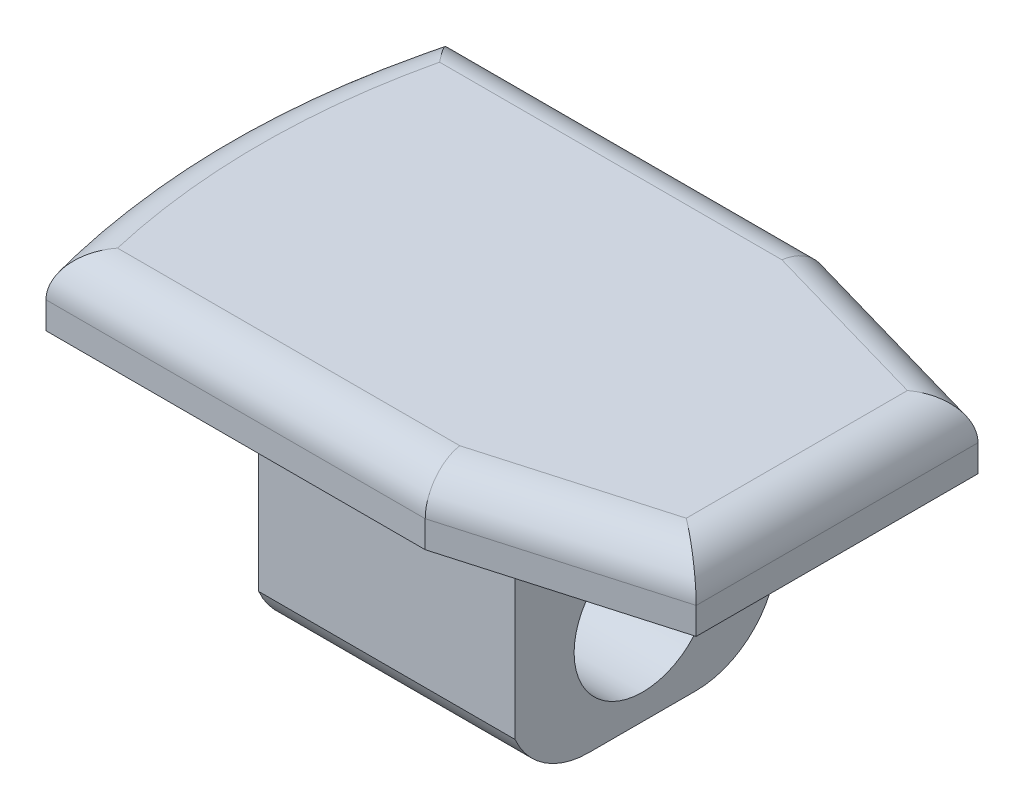
SolidWorks part; units mm, degrees
ref_plane "Front Plane" through (0, 0, 0) normal (0, 0, 1) x (1, 0, 0)
ref_plane "Top Plane" through (0, 0, 0) normal (0, 1, 0) x (1, 0, 0)
ref_plane "Right Plane" through (0, 0, 0) normal (1, 0, 0) x (0, 0, -1)
sketch "Sketch1" plane through (0, 0, 0) normal (0, 1, 0) x (1, 0, 0)
  line L0 (-34.3395, 50.6226) -> (-20.2094, 50.6226)
  line L1 (-20.2094, 50.6226) -> (-12.3627, 48.3726)
  line L2 (-12.3627, 48.3726) -> (-12.3627, 37.8726)
  line L3 (-12.3627, 37.8726) -> (-20.2094, 35.6226)
  line L4 (-20.2094, 35.6226) -> (-34.3395, 35.6226)
  line L5 (-29.3001, 48.1226) -> (-19.3627, 48.1226)
  line L6 (-19.3627, 48.1226) -> (-19.3627, 38.1226)
  line L7 (-19.3627, 38.1226) -> (-29.3001, 38.1226)
  circle A0 centre (-7.3627, 43.1226) radius 28
  circle A1 centre (-7.3627, 43.1226) radius 26
  point P13 (0, 0)
  point P14 (-7.3627, 43.1226)
  point P15 (0, 0)
  point P16 (-34.3395, 50.6226)
  point P17 (0, 0)
  point P18 (-34.3395, 35.6226)
extrude "Boss-Extrude1" add sketch "Sketch1" along normal blind 2.5 contours L0 A1 L5 L6 L7 L4 L3 L2 L1 | A1 L0 A0 L4
ref_plane "Plane1" through (-12.3627, 0, -37.8726) normal (0, 0, 1) x (1, 0, 0)
sketch "Sketch4" plane through (0, 0, 0) normal (0, -1, 0) x (1, 0, 0)
  line L0 (-35.3627, -43.1226) -> (3.6803, -43.1226) construction
  line L1 (-12.3627, -48.3726) -> (-12.3627, -37.8726) construction
  line L2 (-32.8774, -38.1226) -> (-19.3627, -38.1226)
  line L3 (-19.3627, -38.1226) -> (-19.3627, -48.1226)
  line L4 (-19.3627, -48.1226) -> (-32.8774, -48.1226)
  arc A0 (-34.3395, -35.6226) -> (-34.3395, -50.6226) centre (-7.3627, -43.1226) ccw construction
  circle A1 centre (-7.3627, -43.1226) radius 26
  point P5 (-7.3627, -43.1226)
  point P14 (-29.3001, -48.1226)
  point P19 (-29.3001, -38.1226)
  point P20 (0, 0)
  point P21 (0, 0)
  point P22 (-32.8774, -48.1226)
  point P23 (-30.3036, -38.1226)
  point P24 (-32.8774, -38.1226)
  dimension "D1" = 5
extrude "Boss-Extrude2" add sketch "Sketch4" along normal blind 1.5 and the other way blind 1.5
fillet "Fillet1" radius 1.5 6 edges at (-16.286, 2.5, -49.4976) (-12.3627, 2.5, -43.1226) (-16.286, 2.5, -36.7476) (-27.2745, 2.5, -35.6226) (-35.3627, 2.5, -43.1226) (-27.2745, 2.5, -50.6226)
sketch "Sketch5" plane through (0, -1.5, 0) normal (0, -1, 0) x (1, 0, 0)
  line L0 (-29.3001, -38.1226) -> (-19.3627, -38.1226) construction
  line L1 (-19.3627, -48.1226) -> (-29.1627, -48.1226)
  line L2 (-19.3627, -48.1226) -> (-19.3627, -38.1226)
  line L3 (-19.3627, -38.1226) -> (-29.1627, -38.1226)
  line L4 (-29.1627, -48.1226) -> (-29.1627, -38.1226)
  dimension "D1" = 9.8
extrude "Boss-Extrude3" add sketch "Sketch5" along normal blind 7.5
sketch "Sketch6" plane through (-19.3627, 0, 0) normal (1, 0, 0) x (0, 0, -1)
  line L0 (43.1226, 0) -> (43.1226, -9) construction
  line L1 (48.1226, 0) -> (38.1226, 0) construction
  line L2 (48.1226, -9) -> (38.1226, -9) construction
  circle A0 centre (43.1226, -5.5) radius 2.55
  dimension "D1" = 5.5
extrude "Cut-Extrude1" cut sketch "Sketch6" against normal blind 8
sketch "Sketch7" plane through (-27.3627, 0, 0) normal (1, 0, 0) x (0, 0, -1)
  line L1 (39.7279, -4.25) -> (47.1506, -4.25)
  line L2 (39.7279, -4.25) -> (39.7279, -6.75)
  line L3 (39.7279, -6.75) -> (47.1506, -6.75)
  line L4 (47.1506, -4.25) -> (47.1506, -6.75)
  circle A0 centre (43.1226, -5.5) radius 3
  dimension "D1" = 2.5
  dimension "D2" = 1.25
fillet "Fillet2" radius 3 2 edges at (-24.2627, -9, -48.1226) (-24.2627, -9, -38.1226)
sketch "Sketch8" plane through (-29.1627, 0, 0) normal (-1, 0, 0) x (0, 0, 1)
  circle A0 centre (-43.1226, -5.5) radius 2.6
  circle A1 centre (-43.1226, -5.5) radius 3
extrude "Boss-Extrude4" add sketch "Sketch8" against normal blind 0.8
sketch "Sketch9" plane through (0, -9, 0) normal (0, -1, 0) x (-1, 0, 0)
  line L0 (19.3627, 43.1226) -> (33.294, 43.1226) construction
  line L1 (19.3627, 48.1226) -> (19.3627, 38.1226) construction
  line L3 (28.406, 45.8226) -> (29.1627, 45.8226)
  line L4 (28.406, 45.8226) -> (28.406, 40.4226)
  line L5 (28.406, 40.4226) -> (29.1627, 40.4226)
  line L6 (29.1627, 45.8226) -> (29.1627, 40.4226)
  dimension "D1" = 2.7
  dimension "D2" = 2.7
extrude "Cut-Extrude3" cut sketch "Sketch9" against normal blind 3
sketch "Sketch10" plane through (-27.3627, 0, 0) normal (1, 0, 0) x (0, 0, -1)
  circle A0 centre (43.1226, -5.5) radius 3
extrude "Cut-Extrude4" cut sketch "Sketch10" against normal blind 3
sketch "Sketch11" plane through (0, 0, 0) normal (0, -1, 0) x (1, 0, 0)
  line L0 (-19.3627, -38.1226) -> (-32.8774, -38.1226)
  line L1 (-32.8774, -48.1226) -> (-19.3627, -48.1226)
  line L2 (-19.3627, -48.1226) -> (-19.3627, -38.1226)
  line L3 (-19.6127, -38.3726) -> (-32.6708, -38.3726)
  line L4 (-32.6708, -47.8726) -> (-19.6127, -47.8726)
  line L5 (-19.6127, -47.8726) -> (-19.6127, -38.3726)
  arc A0 (-32.8774, -38.1226) -> (-32.8774, -48.1226) centre (-7.3627, -43.1226) ccw
  arc A1 (-32.6708, -38.3726) -> (-32.6708, -47.8726) centre (-7.3627, -43.1226) ccw
  dimension "D1" = 0.25
extrude "Cut-Extrude5" cut sketch "Sketch11" along normal blind 10
